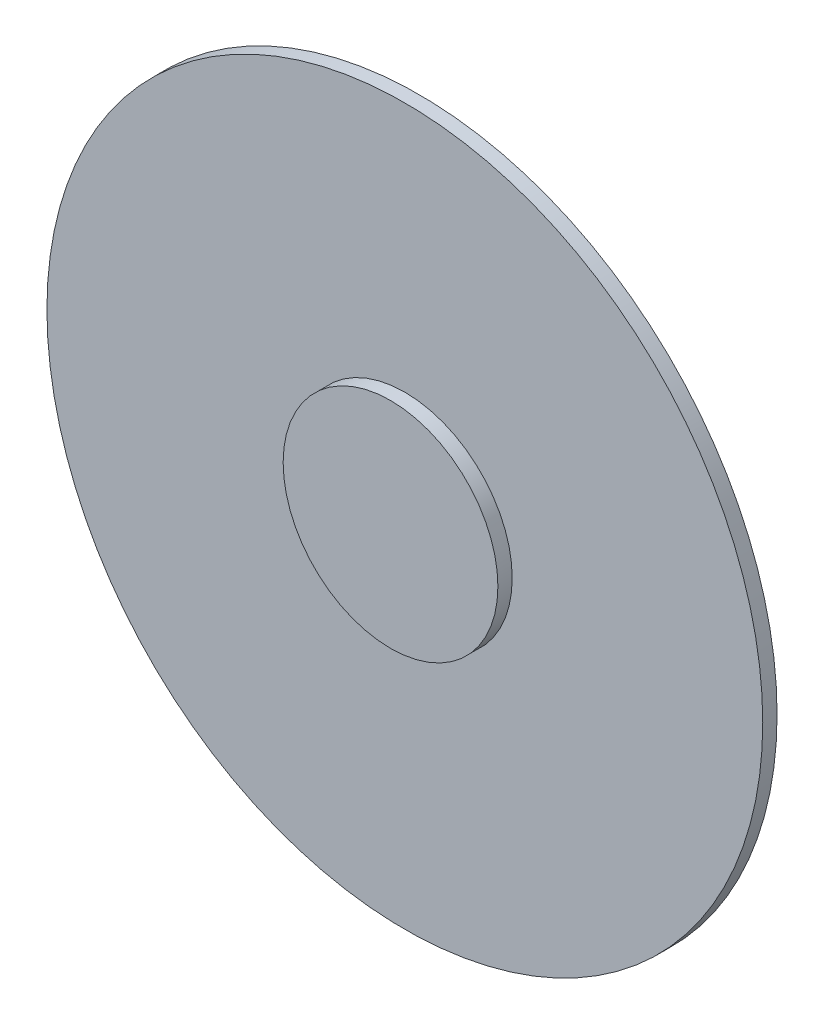
SolidWorks part; units mm, degrees
ref_plane "前视基准面" through (0, 0, 0) normal (0, 0, 1) x (1, 0, 0)
ref_plane "上视基准面" through (0, 0, 0) normal (0, 1, 0) x (1, 0, 0)
ref_plane "右视基准面" through (0, 0, 0) normal (1, 0, 0) x (0, 0, -1)
sketch "草图1" plane through (0, 0, 0) normal (0, 0, 1) x (1, 0, 0)
  circle A0 centre (0, 0) radius 25
  dimension "D1" = 50
extrude "凸台-拉伸1" add sketch "草图1" along normal blind 1
ref_plane "基准面1" through (0, 0, -5) normal (0, 0, -1) x (-1, 0, 0)
sketch "草图2" plane through (0, 0, -5) normal (0, 0, -1) x (-1, 0, 0)
  circle A0 centre (0, 0) radius 10
  dimension "D1" = 20
sketch "草图3" plane through (0, 0, 0) normal (0, 0, -1) x (-1, 0, 0)
  circle A2 centre (0, 0) radius 25
  circle A3 centre (0, 0) radius 25
  dimension "D1" = 0
loft "放样1" add profiles "草图3", "草图2"
sketch "草图4" plane through (0, 0, 1) normal (0, 0, 1) x (1, 0, 0)
  circle A0 centre (0, 0) radius 7.5
  dimension "D1" = 15
extrude "凸台-拉伸2" add sketch "草图4" along normal blind 1
